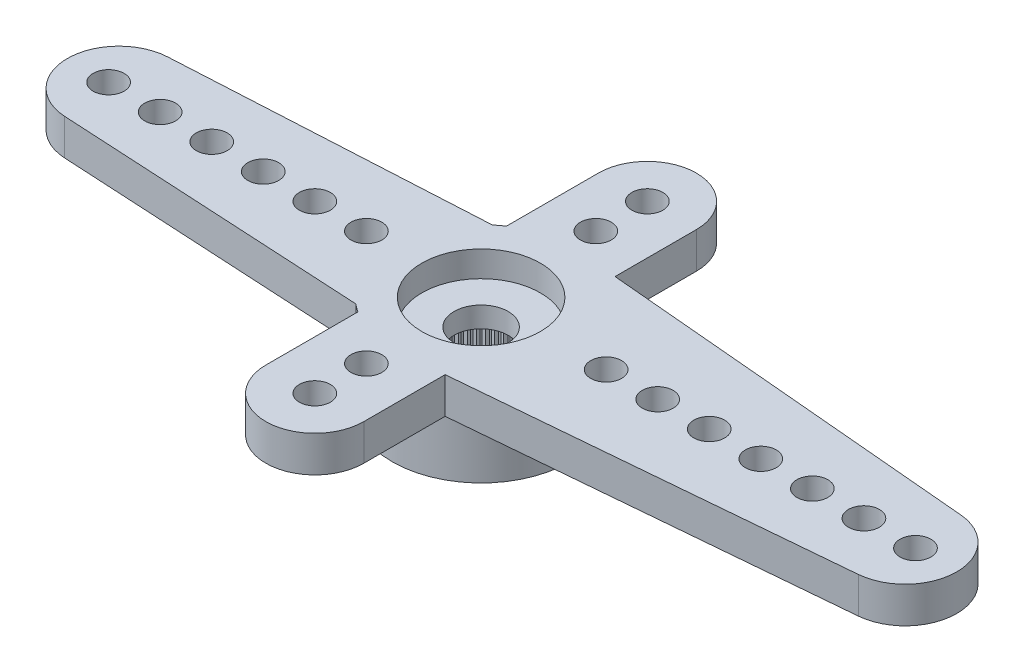
SolidWorks part; units mm, degrees
material "PVC Rígido"
ref_plane "Plano frontal" through (0, 0, 0) normal (0, 0, 1) x (1, 0, 0)
ref_plane "Plano superior" through (0, 0, 0) normal (0, 1, 0) x (1, 0, 0)
ref_plane "Plano direito" through (0, 0, 0) normal (1, 0, 0) x (0, 0, -1)
sketch "Esboço1" plane through (0, 0, 0) normal (0, 1, 0) x (1, 0, 0)
  line L0 (0, 0) -> (-14.05, 0) construction
  line L1 (-14.1591, 1.997) -> (-2.2091, 2.65)
  line L2 (-2.2091, -2.65) -> (-14.1591, -1.997)
  arc A0 (-2.2091, -2.65) -> (-2.2091, 2.65) centre (0, 0) ccw
  arc A1 (-14.1591, 1.997) -> (-14.1591, -1.997) centre (-14.05, 0) ccw
  dimension "D1" = 6.9
  dimension "D2" = 4
  dimension "D3" = 19.5
  dimension "D4" = 5.3
extrude "Ressalto-extrusão1" add sketch "Esboço1" against normal blind 1.4
sketch "Esboço2" plane through (0, -1.4, 0) normal (0, -1, 0) x (1, 0, 0)
  arc A0 (-2.2091, -2.65) -> (-2.2091, 2.65) centre (0, 0) ccw construction
  circle A1 centre (0, 0) radius 3.45
extrude "Ressalto-extrusão2" add sketch "Esboço2" along normal offset from surface (2.4 mm away) 3.8 up to face at (-7.242, 0, 0)
hole_wizard "Furo1" positions "Esboço9" profile "Esboço10" legacy end condition through all
sketch "Esboço9" plane through (0, 0, 0) normal (0, 1, 0) x (1, 0, 0)
  line L1 (-14.45, 0) -> (0, 0) construction
  arc A2 (-14.1591, 1.997) -> (-14.1591, -1.997) centre (-14.05, 0) ccw construction
  point P0 (-14.45, 0)
  point P19 (-16.05, 0)
  dimension "D1" = 1.6
sketch "Esboço10" plane through (-14.45, 0, 0) normal (1, 0, 0) x (0, 0, 1)
  line L0 (0, 0) -> (0, 3.8)
  line L1 (0, 3.8) -> (0.6, 3.8)
  line L2 (0.6, 3.8) -> (0.6, 0)
  line L3 (0.6, 0) -> (0, 0)
  line L4 (0, 110) -> (0, -10) construction
  dimension "Diameter" = 1.2
  dimension "Depth" = 3.8
pattern_linear "Padrão linear1" count 6 spacing 2 along (1, 0, 0) of "Furo1"
sketch "Esboço12" plane through (0, 0, 0) normal (0, 1, 0) x (1, 0, 0)
  line L0 (0.3041, 3.4366) -> (16.6263, 1.9922)
  line L1 (16.6263, -1.9922) -> (0.3041, -3.4366)
  arc A0 (-2.2091, -2.65) -> (-2.2091, 2.65) centre (0, 0) ccw construction
  arc A1 (0.3041, -3.4366) -> (0.3041, 3.4366) centre (0, 0) ccw
  arc A2 (16.6263, 1.9922) -> (16.6263, -1.9922) centre (16.45, 0) cw
  arc A3 (-14.1591, 1.997) -> (-14.1591, -1.997) centre (-14.05, 0) ccw construction
  dimension "D1" = 2
  dimension "D2" = 34.5
extrude "Ressalto-extrusão3" add sketch "Esboço12" against normal up to surface (1.4 mm away) up to face at (-12.45, -1.4, 0.6)
hole_wizard "Furo2" positions "Esboço13" profile "Esboço14" legacy end condition through all
sketch "Esboço13" plane through (0, 0, 0) normal (0, 1, 0) x (1, 0, 0)
  line L0 (0, 0) -> (16.85, 0) construction
  arc A0 (16.6263, -1.9922) -> (16.6263, 1.9922) centre (16.45, 0) ccw construction
  point P0 (16.85, 0)
  point P6 (18.45, 0)
  dimension "D1" = 1.6
sketch "Esboço14" plane through (16.85, 0, 0) normal (1, 0, 0) x (0, 0, 1)
  line L0 (0, 0) -> (0, 3.8)
  line L1 (0, 3.8) -> (0.6, 3.8)
  line L2 (0.6, 3.8) -> (0.6, 0)
  line L3 (0.6, 0) -> (0, 0)
  line L4 (0, 110) -> (0, -10) construction
  dimension "Diameter" = 1.2
  dimension "Depth" = 3.8
pattern_linear "Padrão linear2" count 7 spacing 2 along (-1, 0, 0) of "Furo2"
sketch "Esboço16" plane through (0, 0, 0) normal (0, 1, 0) x (1, 0, 0)
  line L0 (0, -6.45) -> (0, 6.45) construction
  line L1 (-1.9, -6.45) -> (-1.9, 6.45)
  line L2 (1.9, -6.45) -> (1.9, 6.45)
  arc A0 (-1.9, -6.45) -> (1.9, -6.45) centre (0, -6.45) ccw
  arc A1 (1.9, 6.45) -> (-1.9, 6.45) centre (0, 6.45) ccw
  point P2 (0, 0)
  dimension "D2" = 16.7
  dimension "D1" = 3.8
extrude "Ressalto-extrusão4" add sketch "Esboço16" against normal up to surface (1.4 mm away) up to face at (14.85, -1.4, 0.6)
hole_wizard "Furo3" positions "Esboço17" profile "Esboço18" legacy end condition through all
sketch "Esboço17" plane through (0, 0, 0) normal (0, 1, 0) x (1, 0, 0)
  point P0 (0, -6.45)
  point P3 (0, 0)
sketch "Esboço18" plane through (0, 0, 6.45) normal (1, 0, 0) x (0, 0, 1)
  line L0 (0, 0) -> (0, 3.8)
  line L1 (0, 3.8) -> (0.6, 3.8)
  line L2 (0.6, 3.8) -> (0.6, 0)
  line L3 (0.6, 0) -> (0, 0)
  line L4 (0, 110) -> (0, -10) construction
  dimension "Diameter" = 1.2
  dimension "Depth" = 3.8
pattern_linear "Padrão linear3" count 2 spacing 2 along (0, 0, -1) of "Furo3"
pattern_circular "PadrãoCircular1" count 2 over 360 about axis through (0, 0, 0) along (0, 1, 0) of "Padrão linear3", "Furo3"
hole_wizard "Furo4" positions "Esboço3" profile "Esboço4" legacy
sketch "Esboço3" plane through (0, -3.8, 0) normal (0, -1, 0) x (-1, 0, 0)
  point P0 (0, 0)
sketch "Esboço4" plane through (0, -3.8, 0) normal (1, 0, 0) x (0, 0, -1)
  line L0 (0, 0) -> (0, 2)
  line L1 (0, 2) -> (2.475, 2)
  line L2 (2.475, 2) -> (2.475, 0)
  line L3 (2.475, 0) -> (0, 0)
  line L4 (0, 110) -> (0, -10) construction
  dimension "Diameter" = 4.95
  dimension "Depth" = 2
hole_wizard "Furo5" positions "Esboço5" profile "Esboço6" legacy
sketch "Esboço5" plane through (0, 0, 0) normal (0, 1, 0) x (1, 0, 0)
  point P0 (0, 0)
sketch "Esboço6" plane through (0, 0, 0) normal (1, 0, 0) x (0, 0, 1)
  line L0 (0, 0) -> (0, 1)
  line L1 (0, 1) -> (2.3, 1)
  line L2 (2.3, 1) -> (2.3, 0)
  line L3 (2.3, 0) -> (0, 0)
  line L4 (0, 110) -> (0, -10) construction
  dimension "Diameter" = 4.6
  dimension "Depth" = 1
hole_wizard "Furo6" positions "Esboço7" profile "Esboço8" legacy end condition through all
sketch "Esboço7" plane through (0, 0, 0) normal (0, 1, 0) x (1, 0, 0)
  point P0 (0, 0)
sketch "Esboço8" plane through (0, 0, 0) normal (1, 0, 0) x (0, 0, 1)
  line L0 (0, 0) -> (0, 3.8)
  line L1 (0, 3.8) -> (1.05, 3.8)
  line L2 (1.05, 3.8) -> (1.05, 0)
  line L3 (1.05, 0) -> (0, 0)
  line L4 (0, 110) -> (0, -10) construction
  dimension "Diameter" = 2.1
  dimension "Depth" = 3.8
sketch "Esboço11" plane through (0, -3.8, 0) normal (0, -1, 0) x (1, 0, 0)
  line L0 (-0.0981, 2.4731) -> (0, 2.375)
  line L1 (0, 2.375) -> (0.0981, 2.4731)
  line L2 (0, 0) -> (0, 2.475) construction
  circle A0 centre (0, 0) radius 2.375 construction
  circle A1 centre (0, 0) radius 2.475
  arc A2 (0.0981, 2.4731) -> (-0.0981, 2.4731) centre (0, 0) ccw
  dimension "D3" = 4.75
  dimension "D2" = 0.1
  dimension "D1" = 0
extrude "Ressalto-extrusão5" add sketch "Esboço11" against normal up to surface (2 mm away) up to face at (0, -1.8, 1.05)
pattern_circular "PadrãoCircular2" count 60 over 360 about axis through (0, 0, 0) along (0, 1, 0) of "Ressalto-extrusão5"
